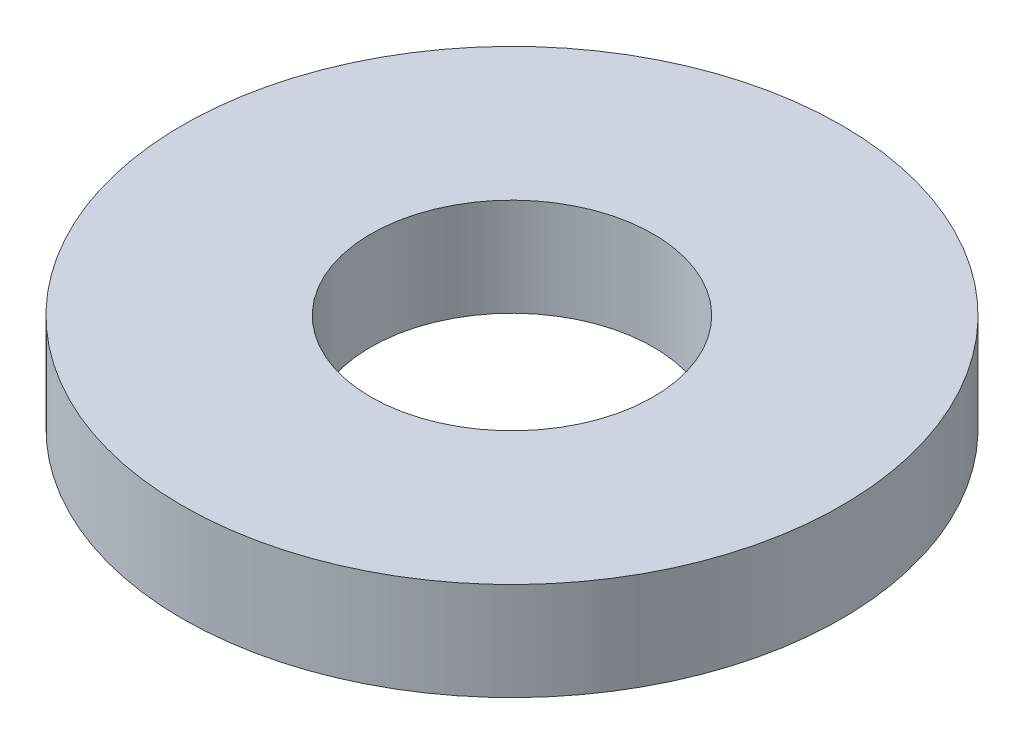
SolidWorks part; units mm, degrees
material "Plain Carbon Steel"
ref_plane "Front Plane" through (0, 0, 0) normal (0, 0, 1) x (1, 0, 0)
ref_plane "Top Plane" through (0, 0, 0) normal (0, 1, 0) x (1, 0, 0)
ref_plane "Right Plane" through (0, 0, 0) normal (1, 0, 0) x (0, 0, -1)
sketch "Sketch1" plane through (0, 0, 0) normal (0, 1, 0) x (1, 0, 0)
  circle A0 centre (0, 0) radius 5.5562
  dimension "OD" = 11.1125
extrude "Boss-Extrude1" add sketch "Sketch1" along normal blind 1.651
sketch "Sketch5" plane through (0, 1.651, 0) normal (0, 1, 0) x (-1, 0, 0)
  circle A0 centre (0, 0) radius 2.3813
  dimension "ID" = 4.7625
extrude "Cut-Extrude1" cut sketch "Sketch5" against normal through all
ref_point "Point1"
